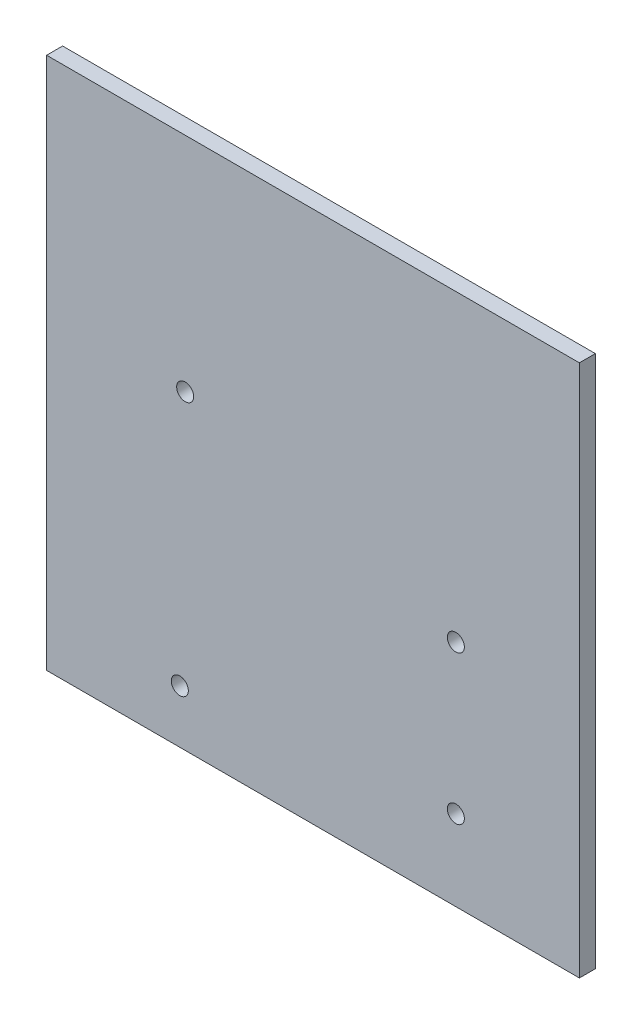
SolidWorks part; units mm, degrees
ref_plane "Front Plane" through (0, 0, 0) normal (0, 0, 1) x (1, 0, 0)
ref_plane "Top Plane" through (0, 0, 0) normal (0, 1, 0) x (1, 0, 0)
ref_plane "Right Plane" through (0, 0, 0) normal (1, 0, 0) x (0, 0, -1)
sketch "Sketch1" plane through (0, 0, 0) normal (0, 0, 1) x (1, 0, 0)
  line L1 (-50, 50) -> (50, 50)
  line L2 (-50, 50) -> (-50, -50)
  line L3 (-50, -50) -> (50, -50)
  line L4 (50, 50) -> (50, -50)
  line L5 (-50, 50) -> (50, -50) construction
  line L6 (-50, -50) -> (50, 50) construction
  point P0 (0, 0)
  point P6 (0, 50)
  dimension "D1" = 100
  dimension "D2" = 100
extrude "Boss-Extrude1" add sketch "Sketch1" along normal blind 3
sketch "Sketch2" plane through (0, 0, 3) normal (0, 0, 1) x (1, 0, 0)
  line L2 (-25.5925, 8.2895) -> (-25, -40) construction
  line L3 (-50, 50) -> (-50, -50) construction
  line L4 (-50, -50) -> (50, -50) construction
  circle A0 centre (26.8075, -34.9) radius 1.6
  circle A1 centre (26.8075, -7) radius 1.6
  circle A2 centre (-25, -40) radius 1.6
  circle A3 centre (-23.9925, 8.2895) radius 1.6
  dimension "D3" = 3.2
  dimension "D1" = 27.9
  dimension "D2" = 48.3
  dimension "D4" = 5.1
  dimension "D5" = 25
  dimension "D6" = 50.8
  dimension "D7" = 10
extrude "Cut-Extrude1" cut sketch "Sketch2" against normal blind 59
